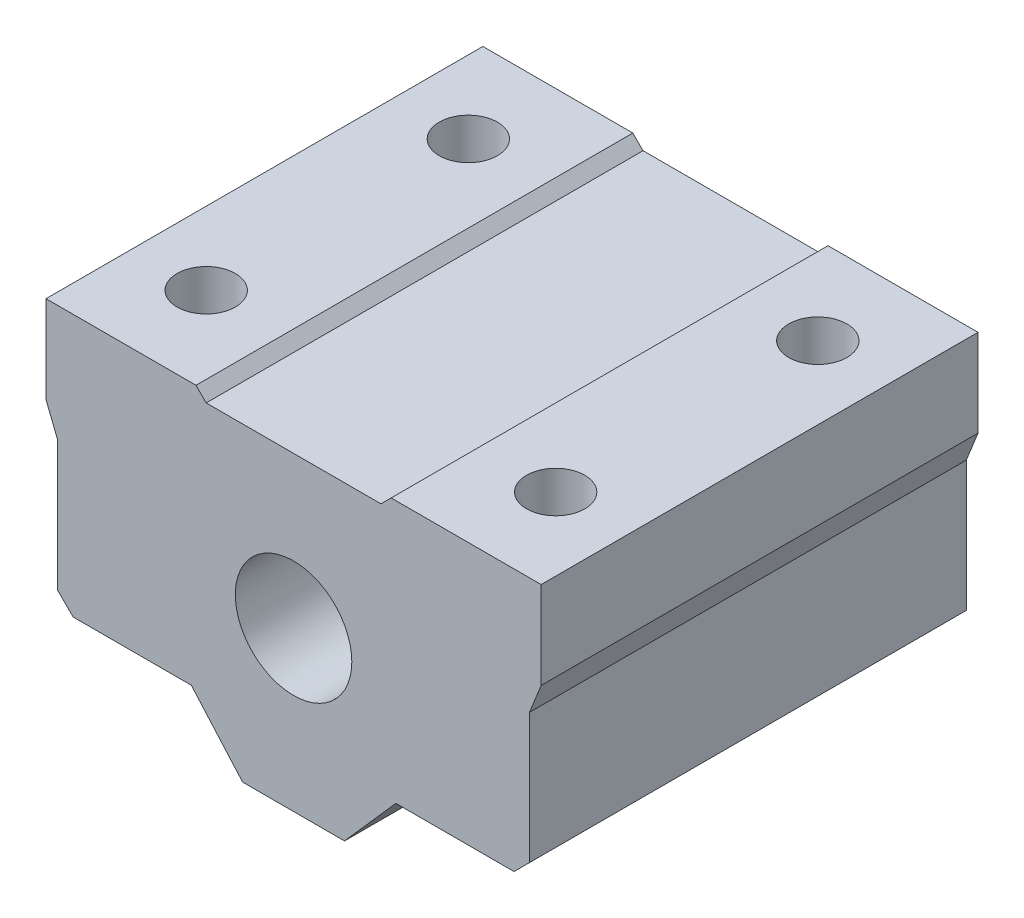
SolidWorks part; units mm, degrees
ref_plane "Front Plane" through (0, 0, 0) normal (0, 0, 1) x (1, 0, 0)
ref_plane "Top Plane" through (0, 0, 0) normal (0, 1, 0) x (1, 0, 0)
ref_plane "Right Plane" through (0, 0, 0) normal (1, 0, 0) x (0, 0, -1)
sketch "Sketch1" plane through (0, 0, 0) normal (0, 0, 1) x (1, 0, 0)
  line L0 (3.5, -10.9039) -> (7.0246, -6.9039)
  line L1 (-17, 11.0961) -> (-6.7, 11.0961)
  line L2 (-17, 11.0961) -> (-17, 5.0961)
  line L3 (3.5, -10.9039) -> (0, -10.9039)
  line L4 (17, 11.0961) -> (17, 5.0961)
  line L5 (-6.2805, 4.0994) -> (6.2805, -4.0994) construction
  line L6 (-6.2805, -4.0994) -> (6.2805, 4.0994) construction
  line L7 (7.0246, -6.9039) -> (15.1393, -6.9039)
  line L8 (-3.5, -10.9039) -> (-7.0246, -6.9039)
  line L9 (-7.0246, -6.9039) -> (-15.1393, -6.9039)
  line L10 (0, -10.9039) -> (0, 0) construction
  line L11 (0, -10.9039) -> (-3.5, -10.9039)
  line L12 (15.1393, -6.9039) -> (16.2, -5.8433)
  line L13 (-16.2, -5.8433) -> (-15.1393, -6.9039)
  line L14 (-17, 5.0961) -> (-16.2, 3.0961)
  line L15 (-16.2, 3.0961) -> (-16.2, -5.8433)
  line L16 (17, 5.0961) -> (16.2, 3.0961)
  line L17 (16.2, -5.8433) -> (16.2, 3.0961)
  line L18 (-6.7, 11.0961) -> (-6, 10.3961)
  line L19 (-6, 10.3961) -> (6, 10.3961)
  line L20 (6, 10.3961) -> (6.7, 11.0961)
  line L21 (6.7, 11.0961) -> (17, 11.0961)
  line L22 (0, 10.3961) -> (0, 0) construction
  circle A0 centre (0, 0) radius 4
  circle A1 centre (0, 0) radius 7.5
  dimension "D1" = 18
  dimension "D3" = 3.5
  dimension "D4" = 34
  dimension "D2" = 22
  dimension "D5" = 6
  dimension "D6" = 8
  dimension "D7" = 12
  dimension "D8" = 0.7
  dimension "D9" = 0.8
extrude "Boss-Extrude1" add sketch "Sketch1" along normal blind 30 contours L21 L20 L19 L18 L1 L2 L14 L15 L13 L9 L8 L11 L3 L0 L7 L12 L17 L16 L4 A1 | A1 A0
sketch "Sketch4" plane through (0, -6.9039, 0) normal (0, -1, 0) x (1, 0, 0)
  line L0 (-7.0246, 30) -> (-15.1393, 30) construction
  line L1 (0, 0) -> (0, 30) construction
  circle A0 centre (-12, 24) radius 2
  circle A1 centre (-12, 6) radius 2
  circle A2 centre (12, 6) radius 2
  circle A3 centre (12, 24) radius 2
  point P4 (-11.082, 30)
  dimension "D1" = 4
  dimension "D2" = 18
  dimension "D3" = 6
  dimension "D4" = 12
  dimension "D5" = 12
extrude "Cut-Extrude1" cut sketch "Sketch4" against normal through all
